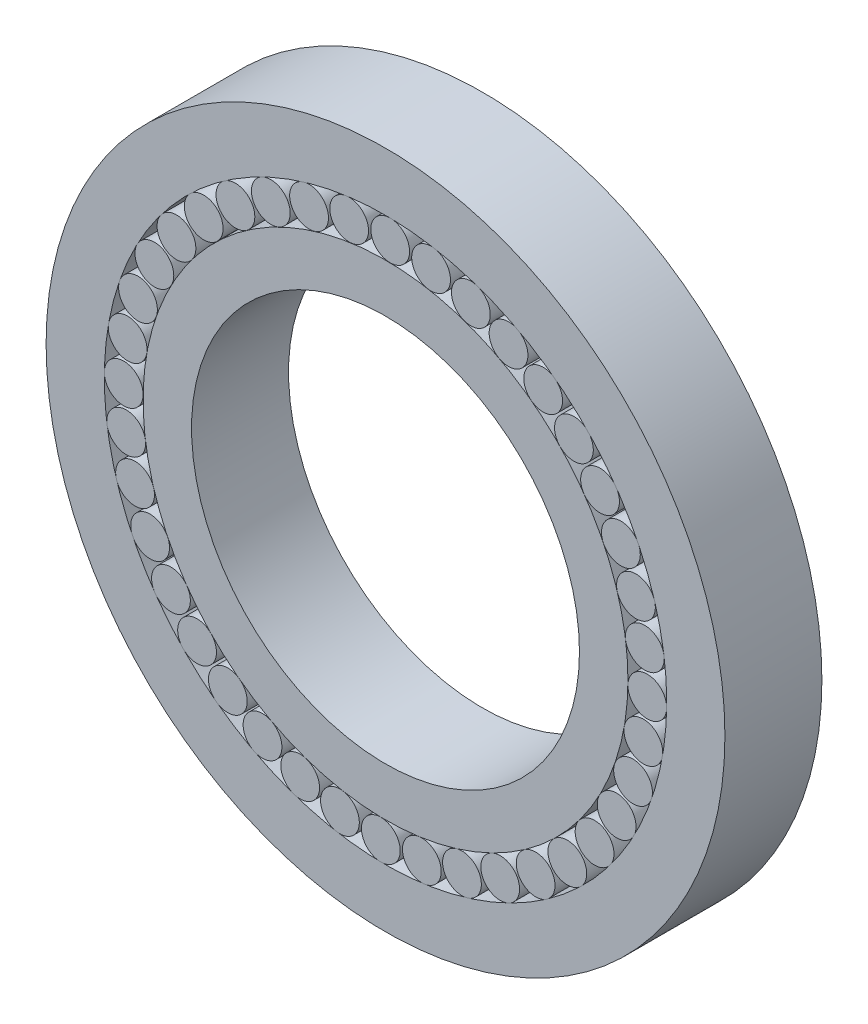
SolidWorks part; units mm, degrees
ref_plane "Front Plane" through (0, 0, 0) normal (0, 0, 1) x (1, 0, 0)
ref_plane "Top Plane" through (0, 0, 0) normal (0, 1, 0) x (1, 0, 0)
ref_plane "Right Plane" through (0, 0, 0) normal (1, 0, 0) x (0, 0, -1)
sketch "Sketch2" plane through (0, 0, 0) normal (0, 0, 1) x (1, 0, 0)
  circle A0 centre (0, 0) radius 35
  circle A1 centre (0, 0) radius 20
  circle A2 centre (0, 0) radius 29
  circle A3 centre (0, 0) radius 25
  circle A4 centre (0.4818, 26.9957) radius 2
  circle A5 centre (4.6989, 26.588) radius 2
  circle A6 centre (8.8003, 25.5256) radius 2
  circle A7 centre (12.6851, 23.8346) radius 2
  circle A8 centre (16.2575, 21.5568) radius 2
  circle A9 centre (19.4295, 18.7482) radius 2
  circle A10 centre (22.1232, 15.4779) radius 2
  circle A11 centre (24.2721, 11.8265) radius 2
  circle A12 centre (25.8233, 7.8839) radius 2
  circle A13 centre (26.7387, 3.7472) radius 2
  circle A14 centre (26.9957, -0.4818) radius 2
  circle A15 centre (26.588, -4.6989) radius 2
  circle A16 centre (25.5256, -8.8003) radius 2
  circle A17 centre (23.8346, -12.6851) radius 2
  circle A18 centre (21.5568, -16.2575) radius 2
  circle A19 centre (18.7482, -19.4295) radius 2
  circle A20 centre (15.4779, -22.1232) radius 2
  circle A21 centre (11.8265, -24.2721) radius 2
  circle A22 centre (7.8839, -25.8233) radius 2
  circle A23 centre (3.7472, -26.7387) radius 2
  circle A24 centre (-0.4818, -26.9957) radius 2
  circle A25 centre (-4.6989, -26.588) radius 2
  circle A26 centre (-8.8003, -25.5256) radius 2
  circle A27 centre (-12.6851, -23.8346) radius 2
  circle A28 centre (-16.2575, -21.5568) radius 2
  circle A29 centre (-19.4295, -18.7482) radius 2
  circle A30 centre (-22.1232, -15.4779) radius 2
  circle A31 centre (-24.2721, -11.8265) radius 2
  circle A32 centre (-25.8233, -7.8839) radius 2
  circle A33 centre (-26.7387, -3.7472) radius 2
  circle A34 centre (-26.9957, 0.4818) radius 2
  circle A35 centre (-26.588, 4.6989) radius 2
  circle A36 centre (-25.5256, 8.8003) radius 2
  circle A37 centre (-23.8346, 12.6851) radius 2
  circle A38 centre (-21.5568, 16.2575) radius 2
  circle A39 centre (-18.7482, 19.4295) radius 2
  circle A40 centre (-15.4779, 22.1232) radius 2
  circle A41 centre (-11.8265, 24.2721) radius 2
  circle A42 centre (-7.8839, 25.8233) radius 2
  circle A43 centre (-3.7472, 26.7387) radius 2
  point P89 (0, 0)
  dimension "D1" = 40
  dimension "D2" = 70
  dimension "D3" = 40
  dimension "D4" = 50
extrude "Boss-Extrude1" add sketch "Sketch2" along normal blind 10 contours A3 A1 | A8 | A9 | A10 | A11 | A12 | A13 | A14 | A15 | A16 | A17 | A18 | A19 | A22 | A23 | A24 | A25 | A26 | A27 | A28 | A29 | A30 | A31 | A32 | A33 | A34 | A40 | A41 | A42 | A43 | A4 | A5 | A6 | A7 | A0 A2 | A20 | A21 | A35 | A36 | A37 | A38 | A39
